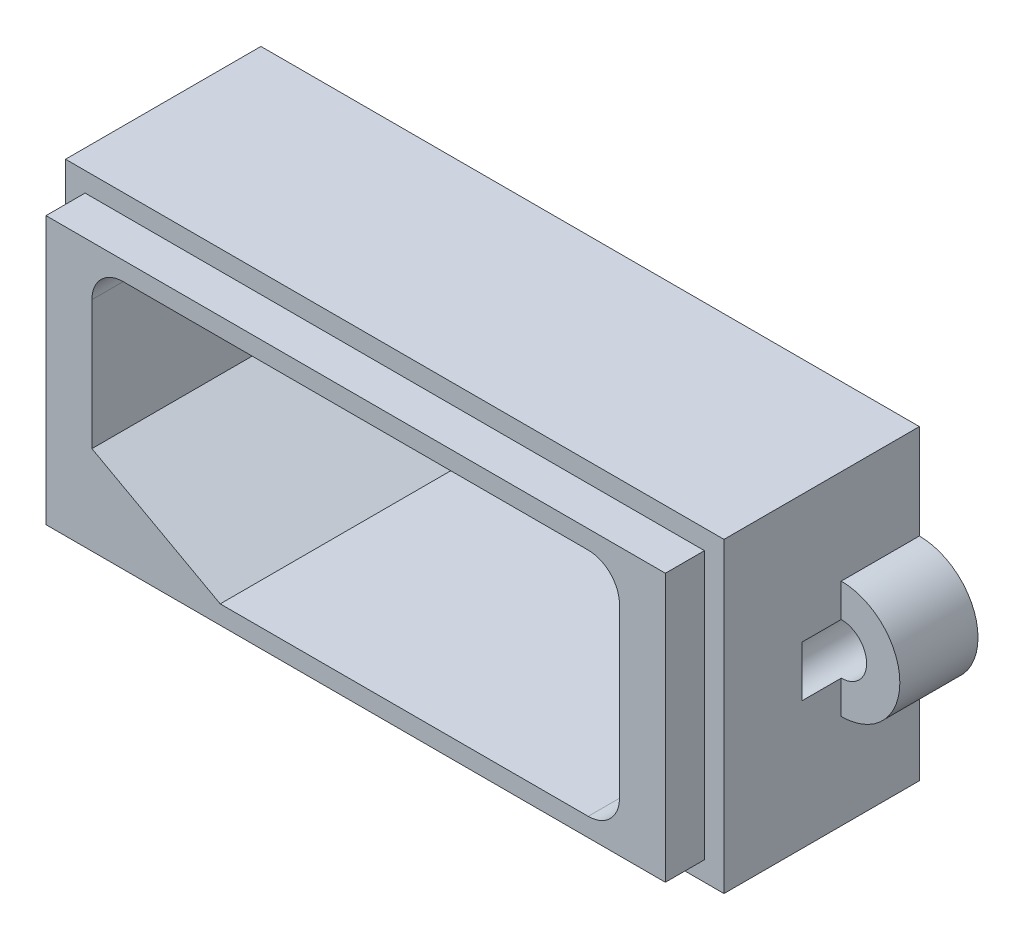
SolidWorks part; units mm, degrees
ref_plane "Alzado" through (0, 0, 0) normal (0, 0, 1) x (1, 0, 0)
ref_plane "Planta" through (0, 0, 0) normal (0, 1, 0) x (1, 0, 0)
ref_plane "Vista lateral" through (0, 0, 0) normal (1, 0, 0) x (0, 0, -1)
sketch "Croquis1" plane through (0, 0, 178) normal (0, 0, -1) x (-1, 0, 0)
  line L0 (30.3504, -11.7749) -> (-3.6496, 4.2251) construction
  line L1 (-3.6496, 4.2251) -> (30.3504, 4.2251) construction
  line L2 (30.2004, -11.6249) -> (-3.4996, -11.6249)
  line L3 (30.2004, -11.6249) -> (30.2004, 4.0751)
  line L4 (30.2004, 4.0751) -> (-3.4996, 4.0751)
  line L5 (-3.4996, -11.6249) -> (-3.4996, 4.0751)
  line L6 (30.2004, -11.6249) -> (-3.4996, 4.0751) construction
  line L7 (30.2004, 4.0751) -> (-3.4996, -11.6249) construction
  line L8 (-3.6496, -11.7749) -> (-3.6496, 4.2251) construction
  point P4 (13.3504, -3.7749)
  dimension "D1" = 0.15
  dimension "D2" = 0.15
extrude "Saliente-Extruir1" add sketch "Croquis1" along normal blind 5
sketch "Croquis2" plane through (0, 0, 178) normal (0, 0, 1) x (1, 0, 0)
  line L0 (-30.2004, -11.6249) -> (3.4996, 4.0751) construction
  line L1 (2.6496, 3.2251) -> (-29.3504, 3.2251) construction
  line L2 (-29.2004, -10.6249) -> (2.4996, -10.6249)
  line L3 (-29.2004, -10.6249) -> (-29.2004, 3.0751)
  line L4 (-29.2004, 3.0751) -> (2.4996, 3.0751)
  line L5 (2.4996, -10.6249) -> (2.4996, 3.0751)
  line L6 (-29.2004, -10.6249) -> (2.4996, 3.0751) construction
  line L7 (-29.2004, 3.0751) -> (2.4996, -10.6249) construction
  line L8 (2.6496, -10.7749) -> (2.6496, 3.2251) construction
  point P4 (-13.3504, -3.7749)
  dimension "D1" = 0.15
  dimension "D2" = 0.15
extrude "Saliente-Extruir2" add sketch "Croquis2" along normal up to surface (2 mm away)
sketch "Croquis3" plane through (0, 0, 180) normal (0, 0, 1) x (1, 0, 0)
  line L0 (-29.2004, -10.6249) -> (2.4996, 3.0751) construction
  line L1 (-29.2004, 3.0751) -> (2.4996, 3.0751) construction
  line L2 (2.4996, -10.6249) -> (2.4996, 3.0751) construction
  line L4 (-25.2504, 2.1251) -> (-1.4504, 2.1251)
  line L5 (-26.8504, 0.5251) -> (-26.8504, -8.0749)
  line L6 (-25.2504, -9.6749) -> (-1.4504, -9.6749)
  line L7 (0.1496, 0.5251) -> (0.1496, -8.0749)
  line L8 (-26.8504, 2.1251) -> (0.1496, -9.6749) construction
  line L9 (-26.8504, -9.6749) -> (0.1496, 2.1251) construction
  arc A0 (-26.8504, -8.0749) -> (-25.2504, -9.6749) centre (-25.2504, -8.0749) ccw
  arc A1 (-1.4504, -9.6749) -> (0.1496, -8.0749) centre (-1.4504, -8.0749) ccw
  arc A2 (-1.4504, 2.1251) -> (0.1496, 0.5251) centre (-1.4504, 0.5251) cw
  arc A3 (-25.2504, 2.1251) -> (-26.8504, 0.5251) centre (-25.2504, 0.5251) ccw
  point P7 (-13.3504, -3.7749)
  dimension "D3" = 1.6
  dimension "D1" = 11.8
  dimension "D2" = 27
extrude "Cortar-Extruir1" cut sketch "Croquis3" against normal blind 10
sketch "Croquis4" plane through (0, 0, 173) normal (0, 0, -1) x (-1, 0, 0)
  line L0 (1.4504, -9.6749) -> (25.2504, -9.6749) construction
  line L1 (-0.1496, 0.5251) -> (-0.1496, -8.0749) construction
  line L2 (25.2504, 2.1251) -> (1.4504, 2.1251) construction
  line L3 (26.8504, -8.0749) -> (26.8504, 0.5251) construction
  line L4 (-3.4996, 4.0751) -> (-3.4996, -11.6249)
  line L5 (-3.4996, -11.6249) -> (30.2004, -11.6249)
  line L6 (30.2004, -11.6249) -> (30.2004, 4.0751)
  line L7 (30.2004, 4.0751) -> (-3.4996, 4.0751)
  line L8 (-3.4996, 4.0751) -> (-3.4996, -11.6249)
  line L9 (-3.4996, -11.6249) -> (30.2004, -11.6249)
  line L10 (30.2004, -11.6249) -> (30.2004, 4.0751)
  line L11 (30.2004, 4.0751) -> (-3.4996, 4.0751)
  line L12 (1.4504, -9.6749) -> (25.2504, -9.6749)
  line L13 (-0.1496, 0.5251) -> (-0.1496, -8.0749)
  line L14 (25.2504, 2.1251) -> (1.4504, 2.1251)
  line L15 (26.8504, -8.0749) -> (26.8504, 0.5251)
  arc A0 (25.2504, -9.6749) -> (26.8504, -8.0749) centre (25.2504, -8.0749) ccw construction
  arc A1 (-0.1496, -8.0749) -> (1.4504, -9.6749) centre (1.4504, -8.0749) ccw construction
  arc A2 (1.4504, 2.1251) -> (-0.1496, 0.5251) centre (1.4504, 0.5251) ccw construction
  arc A3 (26.8504, 0.5251) -> (25.2504, 2.1251) centre (25.2504, 0.5251) ccw construction
  arc A4 (25.2504, -9.6749) -> (26.8504, -8.0749) centre (25.2504, -8.0749) ccw
  arc A5 (-0.1496, -8.0749) -> (1.4504, -9.6749) centre (1.4504, -8.0749) ccw
  arc A6 (1.4504, 2.1251) -> (-0.1496, 0.5251) centre (1.4504, 0.5251) ccw
  arc A7 (26.8504, 0.5251) -> (25.2504, 2.1251) centre (25.2504, 0.5251) ccw
  dimension "D1" = 0
extrude "Saliente-Extruir3" add sketch "Croquis4" along normal blind 5
sketch "Croquis6" plane through (0, 0, 168) normal (0, 0, -1) x (-1, 0, 0)
  line L0 (-3.4996, -11.6249) -> (30.2004, 4.0751) construction
  line L1 (-3.4996, 4.0751) -> (-3.4996, -11.6249) construction
  line L2 (30.2004, -11.6249) -> (30.2004, 4.0751) construction
  circle A0 centre (-3.4996, -3.7749) radius 3
  circle A1 centre (30.2004, -3.7749) radius 3
  dimension "D1" = 6
  dimension "D2" = 6
extrude "Saliente-Extruir5" add sketch "Croquis6" against normal blind 4
sketch "Croquis7" plane through (0, 0, 168) normal (0, 0, -1) x (-1, 0, 0)
  line L0 (20.2841, -9.6749) -> (26.8504, -6.0792)
  line L1 (26.8504, -8.0749) -> (26.8504, -6.0792)
  line L2 (20.2841, -9.6749) -> (25.2504, -9.6749)
  line L3 (1.4504, -9.6749) -> (25.2504, -9.6749) construction
  line L4 (26.8504, -8.0749) -> (26.8504, 0.5251) construction
  line L5 (19.9718, -9.6749) -> (26.8504, -5.9082) construction
  arc A0 (25.2504, -9.6749) -> (26.8504, -8.0749) centre (25.2504, -8.0749) ccw construction
  arc A1 (25.2504, -9.6749) -> (26.8504, -8.0749) centre (25.2504, -8.0749) ccw
  dimension "D1" = 0.3
extrude "Saliente-Extruir6" add sketch "Croquis7" against normal up to surface (12 mm away) up to face at (-13.3504, -3.7749, 180)
sketch "Croquis8" plane through (0, 0, 168) normal (0, 0, -1) x (-1, 0, 0)
  line L0 (-8.2526, -3.7749) -> (35.454, -3.7749) construction
  circle A0 centre (-3.4996, -3.7749) radius 1.3
  circle A1 centre (30.2004, -3.7749) radius 1.3
  point P8 (-3.4996, -3.7749)
  dimension "D1" = 2.6
  dimension "D2" = 2.6
extrude "Cortar-Extruir2" cut sketch "Croquis8" against normal blind 6
